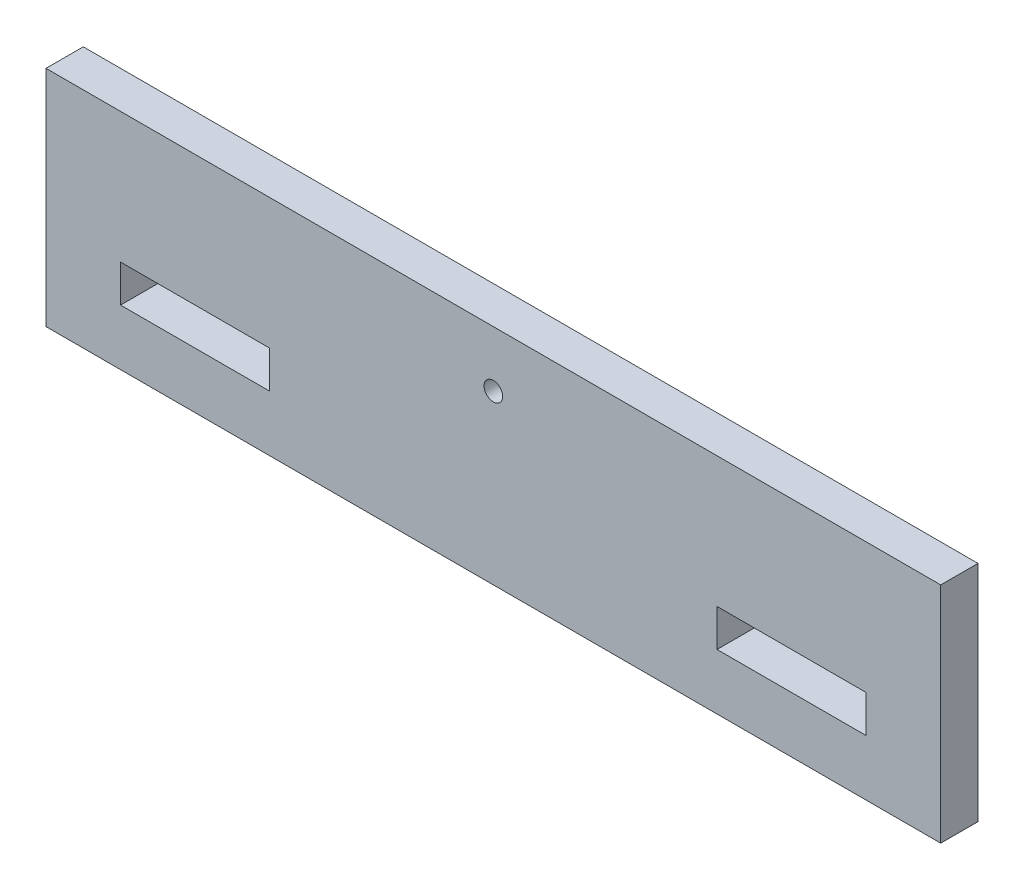
SolidWorks part; units mm, degrees
ref_plane "Front Plane" through (0, 0, 0) normal (0, 0, 1) x (1, 0, 0)
ref_plane "Top Plane" through (0, 0, 0) normal (0, 1, 0) x (1, 0, 0)
ref_plane "Right Plane" through (0, 0, 0) normal (1, 0, 0) x (0, 0, -1)
sketch "Sketch1" plane through (0, 0, 0) normal (0, 0, 1) x (1, 0, 0)
  line L0 (6.35, 38.1) -> (0, 38.1)
  line L1 (6.35, 0) -> (146.05, 0)
  line L2 (6.35, 38.1) -> (146.05, 38.1)
  line L3 (0, 25.4) -> (0, 12.7)
  line L4 (152.4, 25.4) -> (152.4, 12.7)
  line L5 (0, 25.4) -> (0, 38.1)
  line L6 (0, 12.7) -> (0, 0)
  line L7 (0, 0) -> (6.35, 0)
  line L8 (146.05, 38.1) -> (152.4, 38.1)
  line L9 (152.4, 12.7) -> (152.4, 0)
  line L10 (152.4, 38.1) -> (152.4, 25.4)
  line L11 (152.4, 0) -> (146.05, 0)
extrude "Boss-Extrude1" add sketch "Sketch1" along normal blind 6.35
sketch "Sketch2" plane through (0, 0, 6.35) normal (0, 0, 1) x (1, 0, 0)
  line L1 (12.7, 15.875) -> (38.1, 15.875)
  line L2 (12.7, 15.875) -> (12.7, 9.525)
  line L3 (12.7, 9.525) -> (38.1, 9.525)
  line L4 (38.1, 15.875) -> (38.1, 9.525)
extrude "Cut-Extrude1" cut sketch "Sketch2" against normal blind 6.35
sketch "Sketch3" plane through (0, 0, 6.35) normal (0, 0, 1) x (1, 0, 0)
  line L1 (114.3, 9.525) -> (139.7, 9.525)
  line L2 (114.3, 9.525) -> (114.3, 15.875)
  line L3 (114.3, 15.875) -> (139.7, 15.875)
  line L4 (139.7, 9.525) -> (139.7, 15.875)
extrude "Cut-Extrude2" cut sketch "Sketch3" against normal blind 6.35
sketch "Sketch4" plane through (0, 0, 6.35) normal (0, 0, 1) x (1, 0, 0)
  circle A0 centre (76.2, 28.575) radius 1.5875
extrude "Cut-Extrude4" cut sketch "Sketch4" against normal blind 6.35
